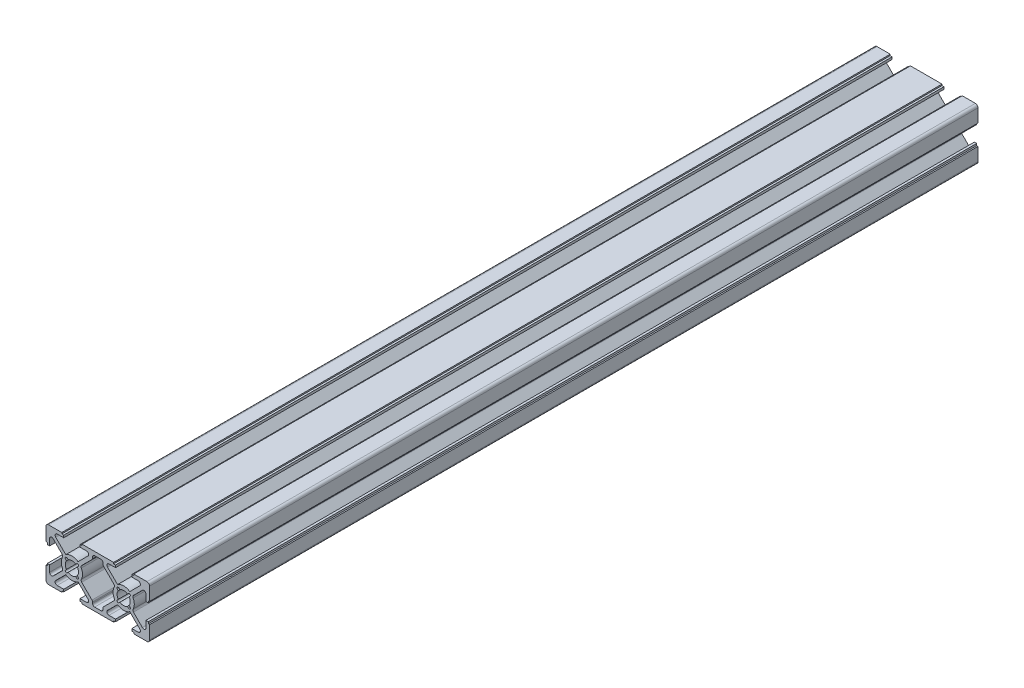
SolidWorks part; units mm, degrees
material "6063-T6"
ref_plane "Ön Düzlem" through (0, 0, 0) normal (0, 0, 1) x (1, 0, 0)
ref_plane "Üst Düzlem" through (0, 0, 0) normal (0, 1, 0) x (1, 0, 0)
ref_plane "Sağ Düzlem" through (0, 0, 0) normal (1, 0, 0) x (0, 0, -1)
sketch "Çizim3" plane through (0, 0, 0) normal (0, 0, 1) x (1, 0, 0)
  line L0 (20, 20) -> (20, 0) construction
  line L1 (0, 0) -> (40, 0) construction
  line L2 (1, 0) -> (6.1, 0)
  line L3 (0, 20) -> (40, 20) construction
  line L4 (40, 0) -> (40, 20) construction
  line L5 (26.1, 0) -> (26.1, 0.5)
  line L6 (0, 0) -> (20, 20) construction
  line L7 (20, 20) -> (40, 0) construction
  line L8 (0, 20) -> (20, 0) construction
  line L9 (20, 0) -> (40, 20) construction
  line L10 (0, 6.1) -> (0.5, 6.1)
  line L11 (0.5, 6.1) -> (0.5, 6.85)
  line L12 (0.5, 6.85) -> (1.4, 6.85)
  line L13 (1.4, 6.85) -> (1.4, 4.3213)
  line L14 (4.3213, 1.4) -> (6.85, 1.4)
  line L15 (6.85, 1.4) -> (6.85, 0.5)
  line L16 (6.85, 0.5) -> (6.1, 0.5)
  line L17 (6.1, 0.5) -> (6.1, 0)
  line L18 (0, 20) -> (0, 0) construction
  line L19 (0, 1) -> (0, 6.1)
  line L20 (6.85, 18.6) -> (6.85, 19.5)
  line L21 (6.85, 19.5) -> (6.1, 19.5)
  line L22 (1, 20) -> (6.1, 20)
  line L23 (4.3213, 18.6) -> (6.85, 18.6)
  line L24 (0, 19) -> (0, 13.9)
  line L25 (1.4, 13.15) -> (1.4, 15.6787)
  line L26 (0.5, 13.15) -> (1.4, 13.15)
  line L27 (0.5, 13.9) -> (0.5, 13.15)
  line L28 (0, 13.9) -> (0.5, 13.9)
  line L29 (6.1, 19.5) -> (6.1, 20)
  line L30 (70.8333, 107.5) -> (354.1667, 107.5) construction
  line L31 (2.7657, 16.2444) -> (6.6485, 12.3616)
  line L32 (3.7556, 17.2343) -> (7.6384, 13.3515)
  line L33 (3.7556, 2.7657) -> (7.6384, 6.6485)
  line L34 (2.7657, 3.7556) -> (6.6485, 7.6384)
  line L35 (0.495, 20.495) -> (20.495, 0.495) construction
  line L36 (-0.495, 19.505) -> (19.505, -0.495) construction
  line L37 (-0.495, 0.495) -> (19.505, 20.495) construction
  line L38 (0.495, -0.495) -> (20.495, 19.505) construction
  line L39 (26.1, 20) -> (13.9, 20)
  line L40 (13.9, 20) -> (13.9, 19.5)
  line L41 (13.9, 19.5) -> (13.15, 19.5)
  line L42 (13.15, 19.5) -> (13.15, 18.6)
  line L43 (13.15, 18.6) -> (15.6787, 18.6)
  line L44 (21.2103, 18.6) -> (18.7897, 18.6)
  line L45 (17.9897, 17.8) -> (17.9897, 17.3311)
  line L46 (26.1, 0) -> (13.9, 0)
  line L47 (13.9, 0) -> (13.9, 0.5)
  line L48 (13.9, 0.5) -> (13.15, 0.5)
  line L49 (13.15, 0.5) -> (13.15, 1.4)
  line L50 (13.15, 1.4) -> (15.6787, 1.4)
  line L51 (18.7897, 1.4) -> (21.2103, 1.4)
  line L52 (17.9897, 2.2) -> (17.9897, 2.6689)
  line L53 (8.2011, 12.4438) -> (8.5527, 12.0922)
  line L54 (7.5562, 11.7989) -> (7.9078, 11.4473)
  line L55 (12.3616, 13.3515) -> (16.2444, 17.2343)
  line L56 (13.3515, 12.3616) -> (17.7554, 16.7654)
  line L57 (7.5562, 8.2011) -> (7.9078, 8.5527)
  line L58 (8.2011, 7.5562) -> (8.5527, 7.9078)
  line L59 (12.3616, 6.6485) -> (16.2444, 2.7657)
  line L60 (13.3515, 7.6384) -> (17.7554, 3.2346)
  line L61 (26.1, 0.5) -> (26.85, 0.5)
  line L62 (12.0922, 8.5527) -> (12.4438, 8.2011)
  line L63 (11.4473, 12.0922) -> (11.7989, 12.4438)
  line L64 (12.0922, 11.4473) -> (12.4438, 11.7989)
  line L65 (11.4473, 7.9078) -> (11.7989, 7.5562)
  line L66 (26.85, 0.5) -> (26.85, 1.4)
  line L67 (26.85, 1.4) -> (24.3213, 1.4)
  line L68 (22.0103, 2.2) -> (22.0103, 2.6689)
  line L69 (26.6485, 7.6384) -> (22.2446, 3.2346)
  line L70 (27.6384, 6.6485) -> (23.7556, 2.7657)
  line L71 (36.2444, 2.7657) -> (32.3616, 6.6485)
  line L72 (37.2343, 3.7556) -> (33.3515, 7.6384)
  line L73 (35.6787, 1.4) -> (33.15, 1.4)
  line L74 (33.15, 1.4) -> (33.15, 0.5)
  line L75 (33.15, 0.5) -> (33.9, 0.5)
  line L76 (33.9, 0.5) -> (33.9, 0)
  line L77 (39, 0) -> (33.9, 0)
  line L78 (40, 1) -> (40, 6.1)
  line L79 (38.6, 6.85) -> (38.6, 4.3213)
  line L80 (39.5, 6.85) -> (38.6, 6.85)
  line L81 (39.5, 6.1) -> (39.5, 6.85)
  line L82 (40, 6.1) -> (39.5, 6.1)
  line L83 (26.1, 20) -> (26.1, 19.5)
  line L84 (26.1, 19.5) -> (26.85, 19.5)
  line L85 (26.85, 19.5) -> (26.85, 18.6)
  line L86 (26.85, 18.6) -> (24.3213, 18.6)
  line L87 (26.6485, 12.3616) -> (22.2446, 16.7654)
  line L88 (27.6384, 13.3515) -> (23.7556, 17.2343)
  line L89 (22.0103, 17.8) -> (22.0103, 17.3311)
  line L90 (27.9078, 11.4473) -> (27.5562, 11.7989)
  line L91 (27.9078, 8.5527) -> (27.5562, 8.2011)
  line L92 (28.5527, 7.9078) -> (28.2011, 7.5562)
  line L93 (31.7989, 7.5562) -> (31.4473, 7.9078)
  line L94 (32.4438, 8.2011) -> (32.0922, 8.5527)
  line L95 (32.4438, 11.7989) -> (32.0922, 11.4473)
  line L96 (31.7989, 12.4438) -> (31.4473, 12.0922)
  line L97 (36.2444, 17.2343) -> (32.3616, 13.3515)
  line L98 (35.6787, 18.6) -> (33.15, 18.6)
  line L99 (33.15, 18.6) -> (33.15, 19.5)
  line L100 (33.15, 19.5) -> (33.9, 19.5)
  line L101 (33.9, 19.5) -> (33.9, 20)
  line L102 (37.2343, 16.2444) -> (33.3515, 12.3616)
  line L103 (38.6, 13.15) -> (38.6, 15.6787)
  line L104 (39.5, 13.15) -> (38.6, 13.15)
  line L105 (39.5, 13.9) -> (39.5, 13.15)
  line L106 (40, 13.9) -> (39.5, 13.9)
  line L107 (40, 19) -> (40, 13.9)
  line L108 (39, 20) -> (33.9, 20)
  line L109 (28.5527, 12.0922) -> (28.2011, 12.4438)
  arc A0 (7.9078, 11.4473) -> (7.9078, 8.5527) centre (10, 10) ccw
  arc A1 (2.7657, 16.2444) -> (1.4, 15.6787) centre (2.2, 15.6787) ccw
  arc A2 (3.7556, 2.7657) -> (4.3213, 1.4) centre (4.3213, 2.2) ccw
  arc A3 (2.7657, 3.7556) -> (1.4, 4.3213) centre (2.2, 4.3213) cw
  arc A4 (3.7556, 17.2343) -> (4.3213, 18.6) centre (4.3213, 17.8) cw
  arc A5 (15.6787, 18.6) -> (16.2444, 17.2343) centre (15.6787, 17.8) cw
  arc A6 (18.7897, 18.6) -> (17.9897, 17.8) centre (18.7897, 17.8) ccw
  arc A7 (17.9897, 17.3311) -> (17.7554, 16.7654) centre (17.1897, 17.3311) cw
  arc A8 (15.6787, 1.4) -> (16.2444, 2.7657) centre (15.6787, 2.2) ccw
  arc A9 (18.7897, 1.4) -> (17.9897, 2.2) centre (18.7897, 2.2) cw
  arc A10 (17.9897, 2.6689) -> (17.7554, 3.2346) centre (17.1897, 2.6689) ccw
  arc A11 (6.6485, 12.3616) -> (6.6485, 7.6384) centre (10, 10) ccw
  arc A12 (12.3616, 13.3515) -> (7.6384, 13.3515) centre (10, 10) ccw
  arc A13 (7.6384, 6.6485) -> (12.3616, 6.6485) centre (10, 10) ccw
  arc A14 (13.3515, 7.6384) -> (13.3515, 12.3616) centre (10, 10) ccw
  arc A15 (11.4473, 12.0922) -> (8.5527, 12.0922) centre (10, 10) ccw
  arc A16 (8.2011, 12.4438) -> (7.5562, 11.7989) centre (7.8787, 12.1213) ccw
  arc A17 (12.4438, 11.7989) -> (11.7989, 12.4438) centre (12.1213, 12.1213) ccw
  arc A18 (11.7989, 7.5562) -> (12.4438, 8.2011) centre (12.1213, 7.8787) ccw
  arc A19 (7.5562, 8.2011) -> (8.2011, 7.5562) centre (7.8787, 7.8787) ccw
  arc A20 (8.5527, 7.9078) -> (11.4473, 7.9078) centre (10, 10) ccw
  arc A21 (12.0922, 8.5527) -> (12.0922, 11.4473) centre (10, 10) ccw
  arc A22 (21.2103, 1.4) -> (22.0103, 2.2) centre (21.2103, 2.2) ccw
  arc A23 (24.3213, 1.4) -> (23.7556, 2.7657) centre (24.3213, 2.2) cw
  arc A24 (22.0103, 2.6689) -> (22.2446, 3.2346) centre (22.8103, 2.6689) cw
  arc A25 (32.3616, 6.6485) -> (27.6384, 6.6485) centre (30, 10) cw
  arc A26 (37.2343, 3.7556) -> (38.6, 4.3213) centre (37.8, 4.3213) ccw
  arc A27 (36.2444, 2.7657) -> (35.6787, 1.4) centre (35.6787, 2.2) cw
  arc A28 (26.6485, 7.6384) -> (26.6485, 12.3616) centre (30, 10) cw
  arc A29 (21.2103, 18.6) -> (22.0103, 17.8) centre (21.2103, 17.8) cw
  arc A30 (24.3213, 18.6) -> (23.7556, 17.2343) centre (24.3213, 17.8) ccw
  arc A31 (22.0103, 17.3311) -> (22.2446, 16.7654) centre (22.8103, 17.3311) ccw
  arc A32 (28.5527, 12.0922) -> (31.4473, 12.0922) centre (30, 10) cw
  arc A33 (27.5562, 11.7989) -> (28.2011, 12.4438) centre (27.8787, 12.1213) cw
  arc A34 (27.9078, 8.5527) -> (27.9078, 11.4473) centre (30, 10) cw
  arc A35 (31.4473, 7.9078) -> (28.5527, 7.9078) centre (30, 10) cw
  arc A36 (32.4438, 8.2011) -> (31.7989, 7.5562) centre (32.1213, 7.8787) cw
  arc A37 (32.0922, 11.4473) -> (32.0922, 8.5527) centre (30, 10) cw
  arc A38 (31.7989, 12.4438) -> (32.4438, 11.7989) centre (32.1213, 12.1213) cw
  arc A39 (33.3515, 12.3616) -> (33.3515, 7.6384) centre (30, 10) cw
  arc A40 (27.6384, 13.3515) -> (32.3616, 13.3515) centre (30, 10) cw
  arc A41 (36.2444, 17.2343) -> (35.6787, 18.6) centre (35.6787, 17.8) ccw
  arc A42 (37.2343, 16.2444) -> (38.6, 15.6787) centre (37.8, 15.6787) cw
  arc A43 (39, 0) -> (40, 1) centre (39, 1) ccw
  arc A44 (40, 19) -> (39, 20) centre (39, 19) ccw
  arc A45 (0, 1) -> (1, 0) centre (1, 1) ccw
  arc A46 (0, 19) -> (1, 20) centre (1, 19) cw
  arc A48 (28.2011, 7.5562) -> (27.5562, 8.2011) centre (27.8787, 7.8787) cw
  point P10 (20, 10)
  point P109 (20, 1.4)
  point P145 (20, 18.6)
  dimension "D10" = 0.8
  dimension "D11" = 0.8
  dimension "D13" = 0.8
  dimension "D14" = 0.8
  dimension "D16" = 0.8
  dimension "D17" = 0.8
  dimension "D18" = 20
  dimension "D20" = 1
  dimension "D1" = 6.3
  dimension "D2" = 20
  dimension "D3" = 6.1
  dimension "D4" = 0.5
  dimension "D5" = 1.4
  dimension "D6" = 0.7
  dimension "D12" = 6.3
  dimension "D15" = 6.3
  dimension "D19" = 10
  dimension "D7" = 0.7
  dimension "D8" = 0.7
  dimension "D9" = 0.7
extrude "Yükseklik-Ekstrüzyon2" add sketch "Çizim3" along normal mid plane 320 contours L22 L29 L21 L20 L23 A4 L32 A12 L55 A5 L43 L42 L41 L40 L39 L83 L84 L85 L86 A30 L88 A40 L97 A41 L98 L99 L100 L101 L108 A44 L107 L106 L105 L104 L103 A42 L102 A39 L72 A26 L79 L80 L81 L82 L78 A43 L77 L76 L75 L74 L73 A27 L71 A25 L70 A23 L67 L66 L61 L5 L46 L47 L48 L49 L50 A8 L59 A13 L33 A2 L14 L15 L16 L17 L2 A45 L19 L10 L11 L12 L13 A3 L34 A11 L31 A1 L25 L26 L27 L28 L24 A46
fillet "Radyus1" radius 0.8 8 edges at (26.6485, 7.6384, 0) (26.6485, 12.3616, 0) (33.3515, 7.6384, 0) (33.3515, 12.3616, 0) (13.3515, 12.3616, 0) (13.3515, 7.6384, 0) (6.6485, 7.6384, 0) (6.6485, 12.3616, 0)
